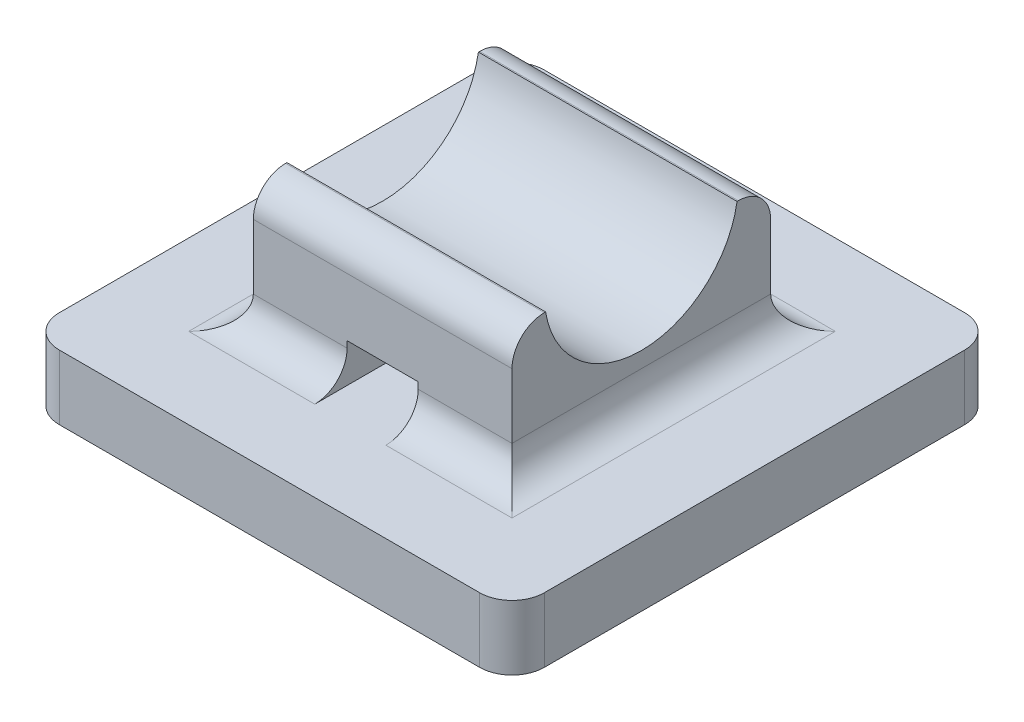
SolidWorks part; units mm, degrees
ref_plane "Alzado" through (0, 0, 0) normal (0, 0, 1) x (1, 0, 0)
ref_plane "Planta" through (0, 0, 0) normal (0, 1, 0) x (1, 0, 0)
ref_plane "Vista lateral" through (0, 0, 0) normal (1, 0, 0) x (0, 0, -1)
sketch "Croquis1" plane through (0, 0, 0) normal (0, 1, 0) x (1, 0, 0)
  line L1 (0, 0) -> (15, 0)
  line L2 (0, 0) -> (0, 15)
  line L3 (0, 15) -> (15, 15)
  line L4 (15, 0) -> (15, 15)
  dimension "D1" = 15
  dimension "D2" = 15
extrude "Saliente-Extruir1" add sketch "Croquis1" along normal blind 2
sketch "Croquis2" plane through (0, 2, 0) normal (0, 1, 0) x (1, 0, 0)
  line L0 (7.5, 15) -> (7.5, 0) construction
  line L1 (15, 15) -> (0, 15) construction
  line L2 (0, 0) -> (15, 0) construction
  line L4 (3.5, 3.5) -> (11.5, 3.5)
  line L5 (3.5, 3.5) -> (3.5, 11.5)
  line L6 (3.5, 11.5) -> (11.5, 11.5)
  line L7 (11.5, 3.5) -> (11.5, 11.5)
  line L8 (3.5, 3.5) -> (11.5, 11.5) construction
  line L9 (3.5, 11.5) -> (11.5, 3.5) construction
  point P6 (7.5, 7.5)
  dimension "D1" = 8
  dimension "D2" = 8
extrude "Saliente-Extruir2" add sketch "Croquis2" along normal blind 4
sketch "Croquis3" plane through (11.5, 0, 0) normal (1, 0, 0) x (0, 0, -1)
  line L0 (7.5, 6.4854) -> (7.5, 2) construction
  line L2 (3.5, 2) -> (11.5, 2) construction
  circle A0 centre (7.5, 6.4854) radius 3
  dimension "D1" = 6
extrude "Cortar-Extruir1" cut sketch "Croquis3" against normal up to surface (8 mm away) up to face at (3.5, 4, -7.5)
sketch "Croquis4" plane through (0, 0, -3.5) normal (0, 0, 1) x (1, 0, 0)
  line L0 (7.5, 2) -> (7.5, 3.3499) construction
  line L1 (3.5, 2) -> (11.5, 2) construction
  line L3 (6.4, 2) -> (8.6, 2)
  line L4 (6.4, 2) -> (6.4, 3.2)
  line L5 (6.4, 3.2) -> (8.6, 3.2)
  line L6 (8.6, 2) -> (8.6, 3.2)
  dimension "D1" = 2.2
  dimension "D2" = 1.2
  dimension "D3" = 1.1
extrude "Cortar-Extruir3" cut sketch "Croquis4" against normal up to surface (8 mm away) up to face at (7.5, 4, -11.5)
fillet "Redondeo1" radius 1 12 edges at (7.5, 6, -3.5) (7.5, 6, -11.5) (15, 1, -15) (15, 1, 0) (0, 1, 0) (0, 1, -15) (3.5, 2, -7.5) (11.5, 2, -7.5) (4.95, 2, -3.5) (10.05, 2, -3.5) (4.95, 2, -11.5) (10.05, 2, -11.5)
